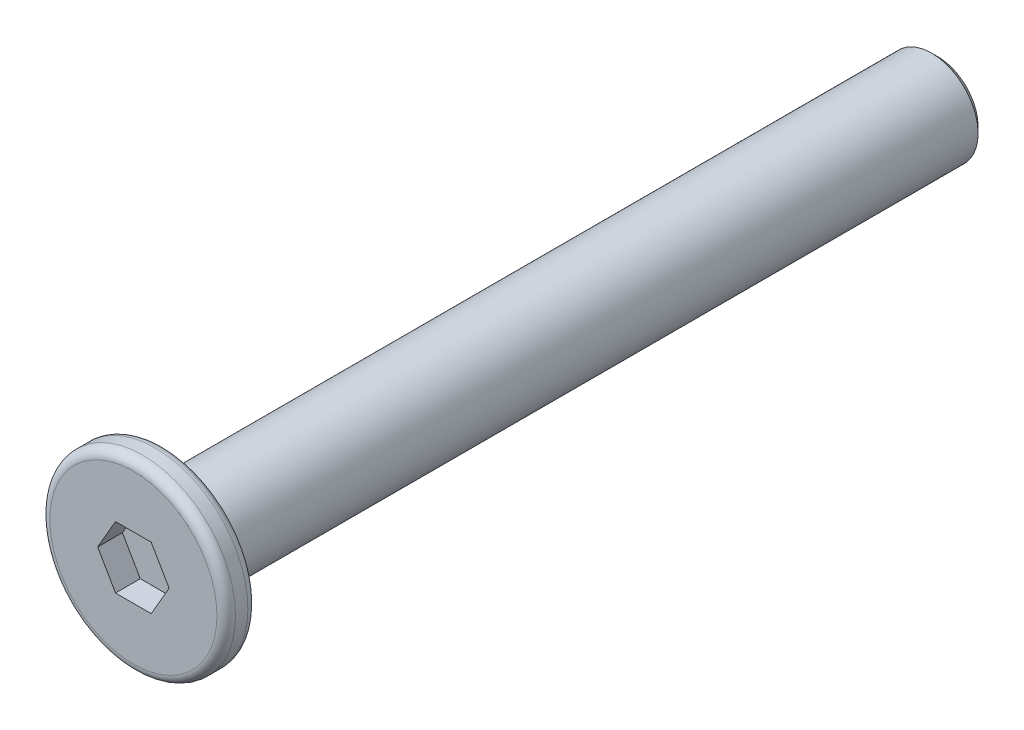
SolidWorks part; units mm, degrees
ref_plane "前视基准面" through (0, 0, 0) normal (0, 0, 1) x (1, 0, 0)
ref_plane "上视基准面" through (0, 0, 0) normal (0, 1, 0) x (1, 0, 0)
ref_plane "右视基准面" through (0, 0, 0) normal (1, 0, 0) x (0, 0, -1)
sketch "草图1" plane through (0, 0, 0) normal (0, 0, 1) x (1, 0, 0)
  circle A0 centre (0, 0) radius 3
  dimension "D1" = 6
extrude "凸台-拉伸1" add sketch "草图1" along normal mid plane 1
sketch "草图2" plane through (0, 0, -0.5) normal (0, 0, -1) x (-1, 0, 0)
  circle A0 centre (0, 0) radius 1.5
  dimension "D1" = 3
extrude "凸台-拉伸2" add sketch "草图2" along normal blind 25
chamfer "倒角1" distance 0.2 angle 45 1 edges at (-1.5, 0, -25.5)
sketch "草图3" plane through (0, 0, 0.5) normal (0, 0, 1) x (1, 0, 0)
  line L1 (1.1547, 0) -> (0.5774, 1)
  line L2 (0.5774, 1) -> (-0.5774, 1)
  line L3 (-0.5774, 1) -> (-1.1547, 0)
  line L4 (-1.1547, 0) -> (-0.5774, -1)
  line L5 (-0.5774, -1) -> (0.5774, -1)
  line L6 (0.5774, -1) -> (1.1547, 0)
  circle A0 centre (0, 0) radius 1 construction
  dimension "D1" = 2
extrude "切除-拉伸1" cut sketch "草图3" against normal blind 0.8
fillet "圆角2" radius 0.3 2 edges at (3, 0, -0.5) (3, 0, 0.5)
